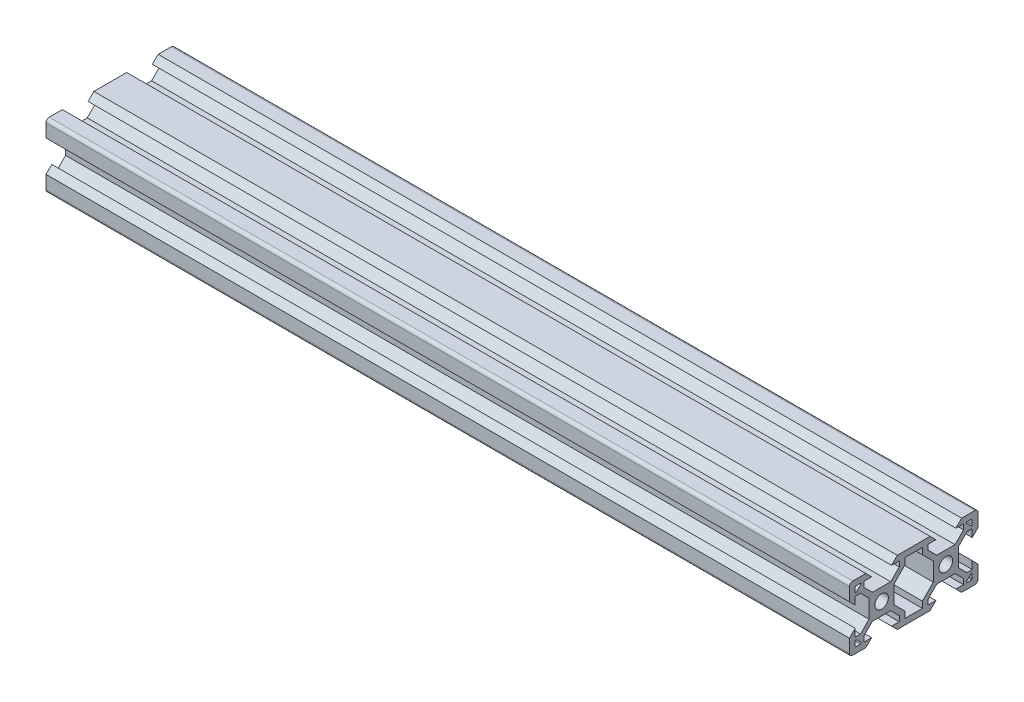
SolidWorks part; units mm, degrees
material "1060 Alloy"
ref_plane "Front Plane" through (0, 0, 0) normal (0, 0, 1) x (1, 0, 0)
ref_plane "Top Plane" through (0, 0, 0) normal (0, 1, 0) x (1, 0, 0)
ref_plane "Right Plane" through (0, 0, 0) normal (1, 0, 0) x (0, 0, -1)
sketch "Sketch4" plane through (0, 0, 0) normal (1, 0, 0) x (0, 0, -1)
  line L0 (-19.2399, 7.0114) -> (20.7601, 7.0114) construction
  dimension "D1" = 40
sketch "Sketch5" plane through (0, 0, 0) normal (1, 0, 0) x (0, 0, -1)
  line L0 (-19.998, 4.9) -> (-18.198, 3.1)
  line L1 (-18.198, 3.1) -> (-18.198, 5.4993)
  line L2 (-18.198, 5.4993) -> (-16.558, 5.4993)
  line L3 (-16.558, 5.4993) -> (-13.9, 2.8413)
  line L4 (-13.9, 2.8413) -> (-13.9, -2.8387)
  line L5 (-13.9, -2.8387) -> (-16.558, -5.4967)
  line L6 (-16.558, -5.4967) -> (-18.198, -5.4967)
  line L7 (-18.198, -5.4967) -> (-18.198, -3.1)
  line L8 (-18.198, -3.1) -> (-19.998, -4.9)
  line L9 (-19.998, -4.9) -> (-19.998, -9)
  line L10 (-18.998, -10) -> (-14.9, -10)
  line L11 (-14.9, -10) -> (-13.1, -8.2)
  line L12 (-13.1, -8.2) -> (-15.5, -8.2)
  line L13 (-15.5, -8.2) -> (-15.5, -6.56)
  line L14 (-15.5, -6.56) -> (-12.84, -3.9)
  line L15 (-12.84, -3.9) -> (-7.16, -3.9)
  line L16 (-7.16, -3.9) -> (-4.5, -6.56)
  line L17 (-4.5, -6.56) -> (-4.5, -8.2)
  line L18 (-4.5, -8.2) -> (-6.9, -8.2)
  line L19 (-6.9, -8.2) -> (-5.1, -10)
  line L20 (-5.1, -10) -> (5.1, -10)
  line L21 (5.1, -10) -> (6.9, -8.2)
  line L22 (6.9, -8.2) -> (4.496, -8.2)
  line L23 (4.496, -8.2) -> (4.496, -6.56)
  line L24 (4.496, -6.56) -> (7.156, -3.9)
  line L25 (7.156, -3.9) -> (12.836, -3.9)
  line L26 (12.836, -3.9) -> (15.496, -6.56)
  line L27 (15.496, -6.56) -> (15.496, -8.2)
  line L28 (15.496, -8.2) -> (13.1, -8.2)
  line L29 (13.1, -8.2) -> (14.9, -10)
  line L30 (14.9, -10) -> (19.002, -10)
  line L31 (20.002, -9) -> (20.002, -4.9)
  line L32 (20.002, -4.9) -> (18.202, -3.1)
  line L33 (18.202, -3.1) -> (18.202, -5.5046)
  line L34 (18.202, -5.5046) -> (16.562, -5.5046)
  line L35 (16.562, -5.5046) -> (13.9, -2.8426)
  line L36 (13.9, -2.8426) -> (13.9, 2.8374)
  line L37 (13.9, 2.8374) -> (16.562, 5.4993)
  line L38 (16.562, 5.4993) -> (18.202, 5.4993)
  line L39 (18.202, 5.4993) -> (18.202, 3.1)
  line L40 (18.202, 3.1) -> (20.002, 4.9)
  line L41 (20.002, 4.9) -> (20.002, 9)
  line L42 (19.002, 10) -> (14.9, 10)
  line L43 (14.9, 10) -> (13.1, 8.2)
  line L44 (13.1, 8.2) -> (15.5013, 8.2)
  line L45 (15.5013, 8.2) -> (15.5013, 6.56)
  line L46 (15.5013, 6.56) -> (12.8413, 3.9)
  line L47 (12.8413, 3.9) -> (7.1613, 3.9)
  line L48 (7.1613, 3.9) -> (4.5013, 6.56)
  line L49 (4.5013, 6.56) -> (4.5013, 8.2)
  line L50 (4.5013, 8.2) -> (6.9, 8.2)
  line L51 (6.9, 8.2) -> (5.1, 10)
  line L52 (5.1, 10) -> (-5.1, 10)
  line L53 (-5.1, 10) -> (-6.9, 8.2)
  line L54 (-6.9, 8.2) -> (-4.5013, 8.2)
  line L55 (-4.5013, 8.2) -> (-4.5013, 6.56)
  line L56 (-4.5013, 6.56) -> (-7.1613, 3.9)
  line L57 (-7.1613, 3.9) -> (-12.8413, 3.9)
  line L58 (-12.8413, 3.9) -> (-15.5013, 6.56)
  line L59 (-15.5013, 6.56) -> (-15.5013, 8.2)
  line L60 (-15.5013, 8.2) -> (-13.1, 8.2)
  line L61 (-13.1, 8.2) -> (-14.9, 10)
  line L62 (-14.9, 10) -> (-18.998, 10)
  line L63 (-19.998, 9) -> (-19.998, 4.9)
  line L64 (6.1, -2.84) -> (6.1, 2.84)
  line L65 (6.1, 2.84) -> (2.7, 6.24)
  line L66 (2.7, 6.24) -> (2.7, 8.2)
  line L67 (2.7, 8.2) -> (-2.7, 8.2)
  line L68 (-2.7, 8.2) -> (-2.7, 6.24)
  line L69 (-2.7, 6.24) -> (-6.1, 2.84)
  line L70 (-6.1, 2.84) -> (-6.1, -2.84)
  line L71 (-6.1, -2.84) -> (-2.7, -6.24)
  line L72 (-2.7, -6.24) -> (-2.7, -8.2)
  line L73 (-2.7, -8.2) -> (2.7, -8.2)
  line L74 (2.7, -8.2) -> (2.7, -6.24)
  line L75 (2.7, -6.24) -> (6.1, -2.84)
  line L76 (0, -8.2) -> (0, 8.2) construction
  line L77 (6.1, 0) -> (-6.1, 0) construction
  line L78 (16.562, 5.4993) -> (15.5013, 6.56) construction
  line L79 (16.5713, 8.2) -> (18.002, 8.2)
  line L81 (17.8606, 6.4279) -> (16.4299, 7.8586)
  line L82 (18.202, 8) -> (18.202, 6.5693)
  line L83 (18.002, 6.5693) -> (18.002, 8) construction
  line L84 (18.002, 8) -> (16.5713, 8) construction
  line L85 (16.5713, 8) -> (18.002, 6.5693) construction
  line L86 (16.5713, -8.2) -> (18.002, -8.2)
  line L87 (18.202, -8) -> (18.202, -6.5693)
  line L88 (17.8606, -6.4279) -> (16.4299, -7.8586)
  line L89 (-17.8606, 6.4279) -> (-16.4299, 7.8586)
  line L90 (-16.5713, 8.2) -> (-18.002, 8.2)
  line L91 (-18.202, 8) -> (-18.202, 6.5693)
  line L92 (-16.5713, -8.2) -> (-18.002, -8.2)
  line L93 (-17.8606, -6.4279) -> (-16.4299, -7.8586)
  line L94 (-18.202, -8) -> (-18.202, -6.5693)
  circle A0 centre (-10, 0) radius 2.1
  circle A1 centre (10, 0) radius 2.1
  arc A2 (-19.998, -9) -> (-18.998, -10) centre (-18.998, -9) ccw
  arc A5 (-18.998, 10) -> (-19.998, 9) centre (-18.998, 9) ccw
  arc A6 (20.002, -9) -> (19.002, -10) centre (19.002, -9) cw
  arc A7 (20.002, 9) -> (19.002, 10) centre (19.002, 9) ccw
  arc A8 (18.002, 8.2) -> (18.202, 8) centre (18.002, 8) cw
  arc A10 (16.4299, 7.8586) -> (16.5713, 8.2) centre (16.5713, 8) cw
  arc A12 (18.202, 6.5693) -> (17.8606, 6.4279) centre (18.002, 6.5693) cw
  arc A13 (16.4299, -7.8586) -> (16.5713, -8.2) centre (16.5713, -8) ccw
  arc A14 (18.002, -8.2) -> (18.202, -8) centre (18.002, -8) ccw
  arc A15 (18.202, -6.5693) -> (17.8606, -6.4279) centre (18.002, -6.5693) ccw
  arc A16 (-18.202, 6.5693) -> (-17.8606, 6.4279) centre (-18.002, 6.5693) ccw
  arc A17 (-16.4299, 7.8586) -> (-16.5713, 8.2) centre (-16.5713, 8) ccw
  arc A18 (-18.002, 8.2) -> (-18.202, 8) centre (-18.002, 8) ccw
  arc A19 (-18.002, -8.2) -> (-18.202, -8) centre (-18.002, -8) cw
  arc A20 (-16.4299, -7.8586) -> (-16.5713, -8.2) centre (-16.5713, -8) cw
  arc A21 (-18.202, -6.5693) -> (-17.8606, -6.4279) centre (-18.002, -6.5693) cw
  dimension "D1" = 4.2
  dimension "D20" = 3.9
  dimension "D27" = 1
  dimension "D40" = 1
  dimension "D41" = 1
  dimension "D42" = 1
  dimension "D45" = 0.2
  dimension "D47" = 1.07
  dimension "D48" = 1.07
  dimension "D49" = 0.2
  dimension "D2" = 20
  dimension "D3" = 10
  dimension "D4" = 5.68
  dimension "D5" = 5.4
  dimension "D6" = 1.96
  dimension "D7" = 45
  dimension "D8" = 1.8
  dimension "D9" = 1.64
  dimension "D10" = 1.8
  dimension "D11" = 40
  dimension "D12" = 20
  dimension "D13" = 3.9
  dimension "D14" = 1.5
  dimension "D15" = 1.5
  dimension "D16" = 3.9
  dimension "D17" = 3.9
  dimension "D18" = 3.9
  dimension "D19" = 3.9
  dimension "D21" = 1.5
  dimension "D22" = 1.5
  dimension "D23" = 1.64
  dimension "D24" = 45
  dimension "D25" = 1.5
  dimension "D26" = 1.8
  dimension "D28" = 6.2
  dimension "D29" = 6.2
  dimension "D30" = 6.2
  dimension "D31" = 6.2
  dimension "D32" = 6.2
  dimension "D33" = 3.1
  dimension "D34" = 3.1
  dimension "D35" = 3.1
  dimension "D36" = 3.1
  dimension "D37" = 6.2
  dimension "D38" = 3.1
  dimension "D39" = 3.1
  dimension "D43" = 1.64
  dimension "D44" = 135
  dimension "D46" = 45
extrude "Boss-Extrude1" add sketch "Sketch5" along normal mid plane 250
